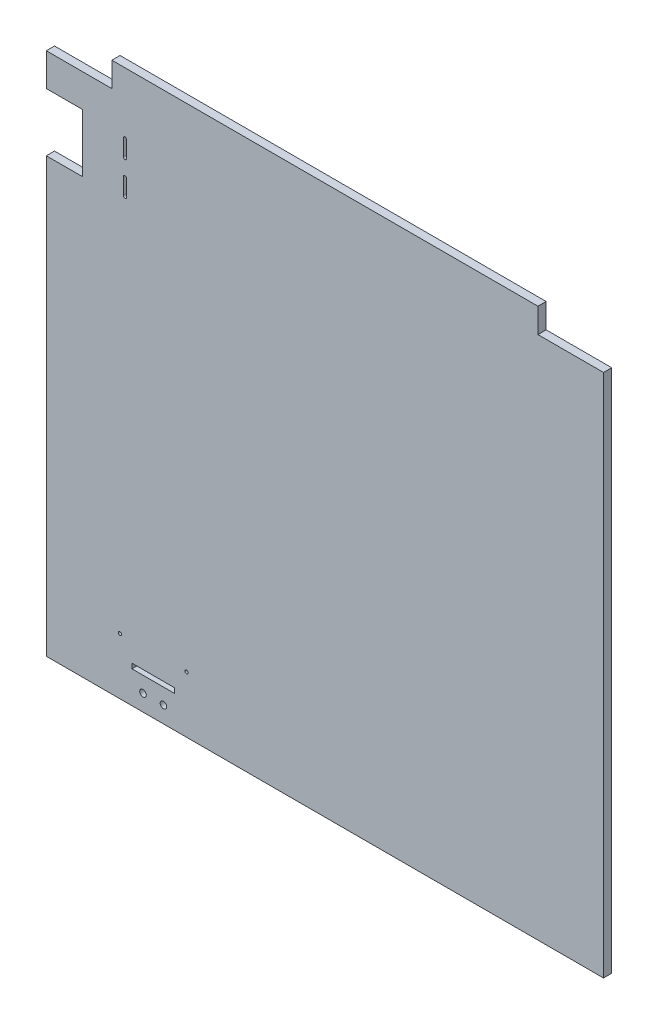
SolidWorks part; units mm, degrees
ref_plane "Plan de face" through (0, 0, 0) normal (0, 0, 1) x (1, 0, 0)
ref_plane "Plan de dessus" through (0, 0, 0) normal (0, 1, 0) x (1, 0, 0)
ref_plane "Plan de droite" through (0, 0, 0) normal (1, 0, 0) x (0, 0, -1)
sketch "Esquisse1" plane through (0, 0, 0) normal (0, 0, 1) x (1, 0, 0)
  line L1 (-340, 335) -> (340, 335)
  line L2 (-340, 335) -> (-340, -335)
  line L3 (-340, -335) -> (340, -335)
  line L4 (340, 335) -> (340, -335)
  dimension "D1" = 680
  dimension "D2" = 340
  dimension "D3" = 670
  dimension "D4" = 335
extrude "Boss.-Extru.1" add sketch "Esquisse1" along normal blind 10
sketch "Esquisse2" plane through (0, 0, 10) normal (0, 0, 1) x (1, 0, 0)
  line L0 (340, 335) -> (-340, 335) construction
  line L1 (-340, 335) -> (-260, 335)
  line L2 (-340, 335) -> (-340, 305)
  line L3 (-340, 305) -> (-260, 305)
  line L4 (-260, 335) -> (-260, 305)
  line L5 (340, 335) -> (260, 335)
  line L6 (340, 335) -> (340, 305)
  line L7 (340, 305) -> (260, 305)
  line L8 (260, 335) -> (260, 305)
  dimension "D1" = 30
  dimension "D2" = 30
  dimension "D3" = 80
  dimension "D4" = 80
extrude "Enlèv. mat.-Extru.1" cut sketch "Esquisse2" against normal through all
sketch "Esquisse3" plane through (0, 0, 10) normal (0, 0, 1) x (1, 0, 0)
  line L1 (-235.5, -290) -> (-183.5, -290)
  line L2 (-235.5, -290) -> (-235.5, -296)
  line L3 (-235.5, -296) -> (-183.5, -296)
  line L4 (-183.5, -290) -> (-183.5, -296)
  line L6 (-340, -335) -> (340, -335) construction
  line L7 (-340, 305) -> (-340, -335) construction
  dimension "D1" = 6
  dimension "D2" = 104.5
  dimension "D3" = 52
  dimension "D5" = 39
extrude "Enlèv. mat.-Extru.2" cut sketch "Esquisse3" against normal through all
sketch "Esquisse4" plane through (0, 0, 10) normal (0, 0, 1) x (1, 0, 0)
  line L0 (-340, -335) -> (340, -335) construction
  line L1 (-340, 305) -> (-340, -335) construction
  line L2 (340, -335) -> (340, 305) construction
  circle A0 centre (-222, -315) radius 4
  circle A1 centre (-197, -315) radius 4
  dimension "D1" = 8
  dimension "D2" = 8
  dimension "D3" = 25
  dimension "D4" = 20
  dimension "D5" = 20
  dimension "D6" = 118
  dimension "D7" = 537
extrude "Enlèv. mat.-Extru.3" cut sketch "Esquisse4" against normal through all
sketch "Esquisse5" plane through (0, 0, 10) normal (0, 0, 1) x (1, 0, 0)
  line L0 (-340, -335) -> (340, -335) construction
  line L1 (-340, 305) -> (-340, -335) construction
  line L3 (340, -335) -> (340, 305) construction
  circle A0 centre (-250, -266) radius 2
  circle A1 centre (-169, -266) radius 2
  dimension "D1" = 4
  dimension "D2" = 4
  dimension "D3" = 81
  dimension "D4" = 69
  dimension "D5" = 90
  dimension "D6" = 509
  dimension "D7" = 69
extrude "Enlèv. mat.-Extru.4" cut sketch "Esquisse5" against normal through all
sketch "Esquisse6" plane through (0, 0, 10) normal (0, 0, 1) x (1, 0, 0)
  line L0 (-340, 305) -> (-340, -335) construction
  line L1 (-340, 265) -> (-296, 265)
  line L2 (-340, 265) -> (-340, 194)
  line L3 (-340, 194) -> (-296, 194)
  line L4 (-296, 265) -> (-296, 194)
  line L5 (-340, 305) -> (-260, 305) construction
  dimension "D1" = 44
  dimension "D2" = 40
  dimension "D3" = 71
extrude "Enlèv. mat.-Extru.5" cut sketch "Esquisse6" against normal through all
sketch "Esquisse7" plane through (0, 0, 10) normal (0, 0, 1) x (1, 0, 0)
  line L0 (-296, 265) -> (-340, 265) construction
  line L1 (-246, 260) -> (-246, 240)
  line L2 (-242, 260) -> (-242, 240)
  line L3 (-246, 219) -> (-246, 199)
  line L4 (-242, 219) -> (-242, 199)
  line L5 (-296, 194) -> (-296, 265) construction
  arc A0 (-242, 260) -> (-246, 260) centre (-244, 260) ccw
  arc A1 (-242, 219) -> (-246, 219) centre (-244, 219) ccw
  arc A2 (-246, 240) -> (-242, 240) centre (-244, 240) ccw
  arc A3 (-246, 199) -> (-242, 199) centre (-244, 199) ccw
  dimension "D1" = 4
  dimension "D2" = 4
  dimension "D3" = 41
  dimension "D4" = 5
  dimension "D5" = 4
  dimension "D6" = 4
  dimension "D7" = 41
  dimension "D8" = 52
extrude "Enlèv. mat.-Extru.6" cut sketch "Esquisse7" against normal through all
